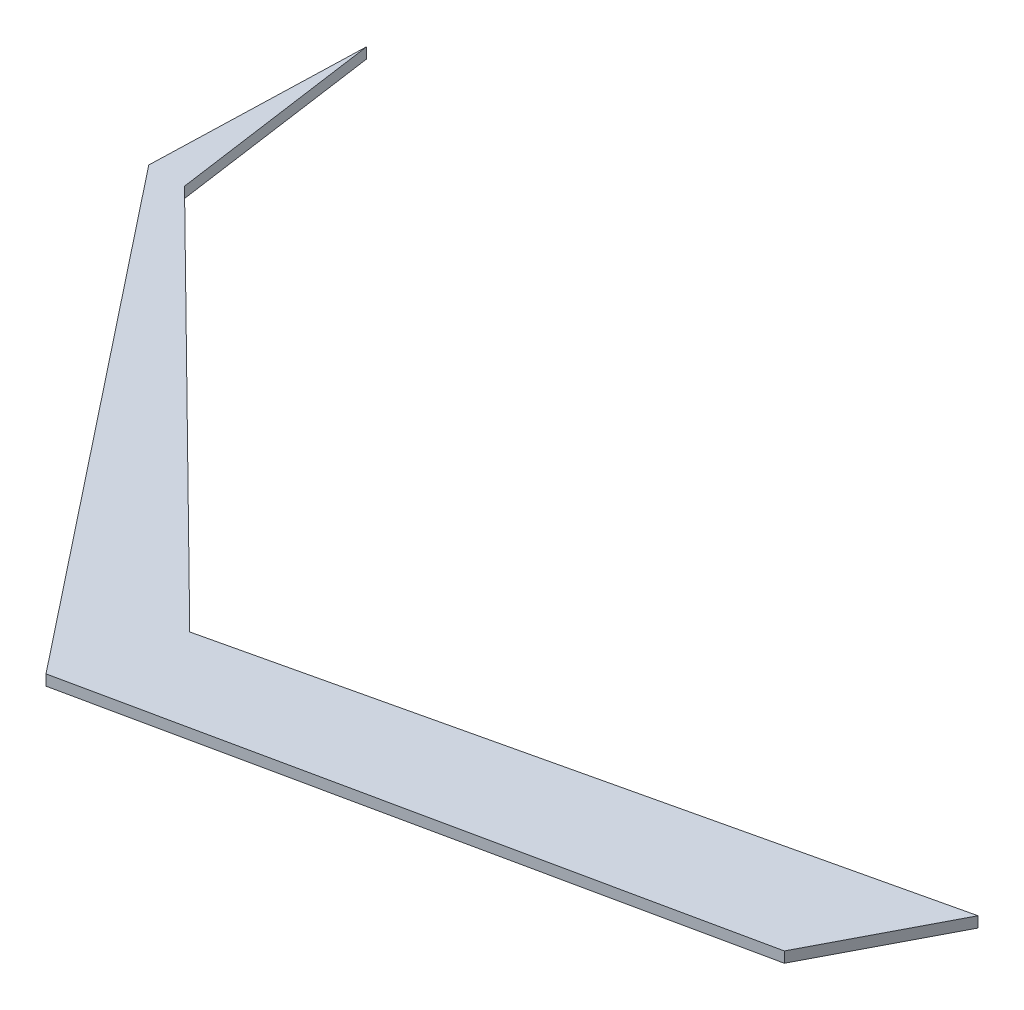
SolidWorks part; units mm, degrees
ref_plane "Plan de face" through (0, 0, 0) normal (0, 0, 1) x (1, 0, 0)
ref_plane "Plan de dessus" through (0, 0, 0) normal (0, 1, 0) x (1, 0, 0)
ref_plane "Plan de droite" through (0, 0, 0) normal (1, 0, 0) x (0, 0, -1)
sketch "Esquisse1" plane through (0, 0, 0) normal (0, 1, 0) x (1, 0, 0)
  line L0 (-71.7109, 131.7552) -> (-72.927, 92.1759)
  line L1 (-72.927, 92.1759) -> (0, 0)
  line L2 (0, 0) -> (114.0873, 24.2009)
  line L3 (114.0873, 24.2009) -> (126.5212, 48.0551)
  line L4 (126.5212, 48.0551) -> (6.6628, 20.2636)
  line L5 (6.6628, 20.2636) -> (-66.1402, 92.0834)
  line L6 (-66.1402, 92.0834) -> (-71.7109, 131.7552)
  point P7 (0, 0)
extrude "Boss.-Extru.1" add sketch "Esquisse1" along normal blind 2
